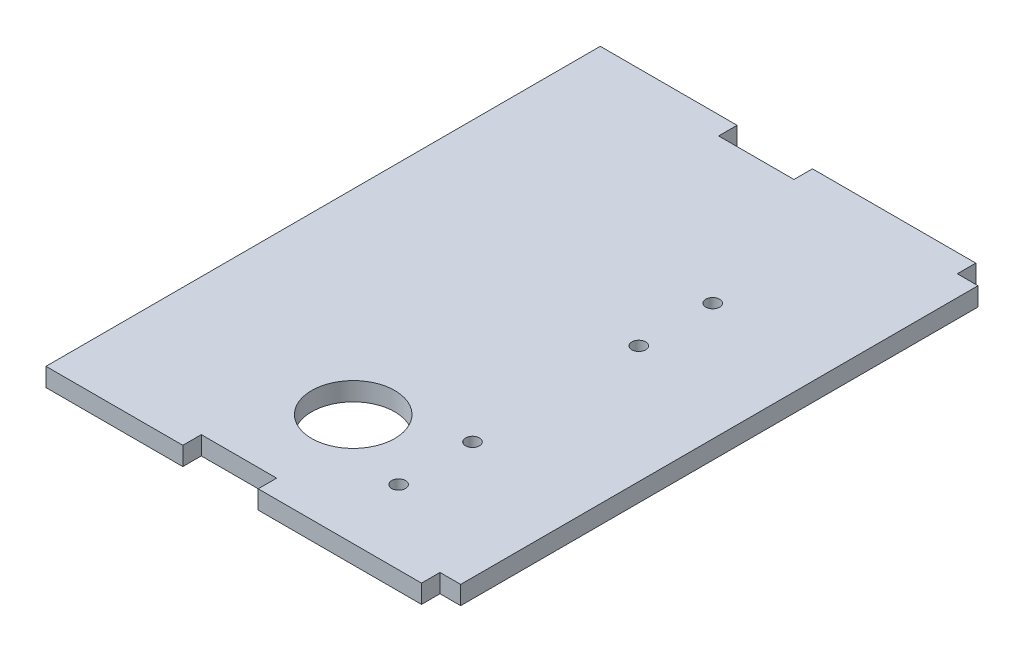
SolidWorks part; units mm, degrees
ref_plane "Front Plane" through (0, 0, 0) normal (0, 0, 1) x (1, 0, 0)
ref_plane "Top Plane" through (0, 0, 0) normal (0, 1, 0) x (1, 0, 0)
ref_plane "Right Plane" through (0, 0, 0) normal (1, 0, 0) x (0, 0, -1)
sketch "Sketch1" plane through (0, 0, 0) normal (0, 1, 0) x (1, 0, 0)
  line L1 (0, 0) -> (304.8, 0)
  line L2 (0, 0) -> (0, 355.6)
  line L3 (0, 355.6) -> (304.8, 355.6)
  line L4 (304.8, 0) -> (304.8, 355.6)
  ellipse E0 centre (166.7242, 64.195) end of major axis (195.2992, 64.195) minor radius 28.574 construction
  ellipse E1 centre (166.7242, 64.195) end of major axis (195.2992, 64.195) minor radius 28.574
  dimension "D1" = 355.6
  dimension "D2" = 304.8
extrude "Boss-Extrude1" add sketch "Sketch1" along normal blind 12.7
sketch "Sketch2" plane through (0, 0, 0) normal (0, -1, 0) x (1, 0, 0)
  line L0 (0, 0) -> (304.8, 0) construction
  line L1 (0, -355.6) -> (0, 0) construction
  circle A0 centre (224.028, -38.1) radius 4.7625
  circle A1 centre (224.028, -88.9) radius 4.7625
  circle A2 centre (224.028, -203.2) radius 4.7625
  circle A3 centre (224.028, -254) radius 4.7625
  dimension "D3" = 88.9
  dimension "D6" = 9.525
  dimension "D1" = 38.1
  dimension "D2" = 224.028
  dimension "D4" = 203.2
  dimension "D5" = 254
  dimension "D7" = 224.028
  dimension "D8" = 224.028
  dimension "D9" = 224.028
extrude "Cut-Extrude1" cut sketch "Sketch2" against normal blind 12.7
sketch "Sketch3" plane through (0, 12.7, 0) normal (0, 1, 0) x (1, 0, 0)
  line L0 (152.4, 355.6) -> (152.4, 250.206) construction
  line L1 (0, 177.8) -> (22.2548, 177.8) construction
  line L2 (14.224, 355.6) -> (126.492, 355.6)
  line L3 (14.224, 355.6) -> (14.224, 368.3)
  line L4 (0, 355.6) -> (0, 0)
  line L5 (0, 0) -> (304.8, 0)
  line L6 (304.8, 0) -> (304.8, 355.6)
  line L7 (304.8, 355.6) -> (0, 355.6)
  line L8 (0, 355.6) -> (0, 0) construction
  line L9 (0, 0) -> (304.8, 0) construction
  line L10 (304.8, 0) -> (304.8, 355.6) construction
  line L11 (304.8, 355.6) -> (0, 355.6) construction
  line L12 (14.224, 368.3) -> (126.492, 368.3)
  line L13 (126.492, 355.6) -> (126.492, 368.3)
  line L14 (290.576, 368.3) -> (178.308, 368.3)
  line L15 (178.308, 355.6) -> (178.308, 368.3)
  line L16 (290.576, 355.6) -> (178.308, 355.6)
  line L17 (290.576, 355.6) -> (290.576, 368.3)
  line L18 (290.576, 0) -> (290.576, -12.7)
  line L19 (290.576, 0) -> (178.308, 0)
  line L20 (178.308, 0) -> (178.308, -12.7)
  line L21 (290.576, -12.7) -> (178.308, -12.7)
  line L22 (14.224, -12.7) -> (126.492, -12.7)
  line L23 (126.492, 0) -> (126.492, -12.7)
  line L24 (14.224, 0) -> (126.492, 0)
  line L25 (14.224, 0) -> (14.224, -12.7)
  dimension "D2" = 25.908
  dimension "D3" = 112.268
  dimension "D4" = 12.7
  dimension "D1" = 0
extrude "Boss-Extrude2" add sketch "Sketch3" against normal blind 12.7
sketch "Sketch4" plane through (0, 0, 0) normal (0, -1, 0) x (1, 0, 0)
  line L20 (0, 0) -> (0, -355.6)
  line L21 (0, -355.6) -> (14.224, -355.6)
  line L22 (14.224, -355.6) -> (14.224, -368.3)
  line L23 (14.224, -368.3) -> (126.492, -368.3)
  line L24 (126.492, -368.3) -> (126.492, -355.6)
  line L25 (126.492, -355.6) -> (178.308, -355.6)
  line L26 (178.308, -355.6) -> (178.308, -368.3)
  line L27 (178.308, -368.3) -> (290.576, -368.3)
  line L28 (290.576, -368.3) -> (290.576, -355.6)
  line L29 (290.576, -355.6) -> (304.8, -355.6)
  line L30 (304.8, -355.6) -> (304.8, 0)
  line L31 (304.8, 0) -> (290.576, 0)
  line L32 (290.576, 0) -> (290.576, 12.7)
  line L33 (290.576, 12.7) -> (178.308, 12.7)
  line L34 (178.308, 12.7) -> (178.308, 0)
  line L35 (178.308, 0) -> (126.492, 0)
  line L36 (126.492, 0) -> (126.492, 12.7)
  line L37 (126.492, 12.7) -> (14.224, 12.7)
  line L38 (14.224, 12.7) -> (14.224, 0)
  line L39 (14.224, 0) -> (0, 0)
  line L40 (0, 0) -> (0, -355.6)
  line L41 (0, -355.6) -> (14.224, -355.6)
  line L42 (14.224, -355.6) -> (14.224, -368.3)
  line L43 (14.224, -368.3) -> (126.492, -368.3)
  line L44 (126.492, -368.3) -> (126.492, -355.6)
  line L45 (126.492, -355.6) -> (178.308, -355.6)
  line L46 (178.308, -355.6) -> (178.308, -368.3)
  line L47 (178.308, -368.3) -> (290.576, -368.3)
  line L48 (290.576, -368.3) -> (290.576, -355.6)
  line L49 (290.576, -355.6) -> (304.8, -355.6)
  line L50 (304.8, -355.6) -> (304.8, 0)
  line L51 (304.8, 0) -> (290.576, 0)
  line L52 (290.576, 0) -> (290.576, 12.7)
  line L53 (290.576, 12.7) -> (178.308, 12.7)
  line L54 (178.308, 12.7) -> (178.308, 0)
  line L55 (178.308, 0) -> (126.492, 0)
  line L56 (126.492, 0) -> (126.492, 12.7)
  line L57 (126.492, 12.7) -> (14.224, 12.7)
  line L58 (14.224, 12.7) -> (14.224, 0)
  line L59 (14.224, 0) -> (0, 0)
  circle A5 centre (224.028, -203.2) radius 4.7625 construction
  circle A6 centre (224.028, -88.9) radius 4.7625 construction
  dimension "D3" = 109.5375
  dimension "D1" = 0
sketch "Sketch5" plane through (0, 0, 0) normal (0, -1, 0) x (1, 0, 0)
  line L0 (-5.9328, 12.7) -> (-5.9328, -368.3)
  line L1 (290.576, 12.7) -> (178.308, 12.7) construction
  line L2 (178.308, -368.3) -> (290.576, -368.3) construction
  line L3 (-5.9328, -368.3) -> (32.4509, -368.3)
  line L4 (32.4509, -368.3) -> (32.4509, 12.7)
  line L5 (32.4509, 12.7) -> (-5.9328, 12.7)
extrude "Cut-Extrude2" cut sketch "Sketch5" against normal through all
